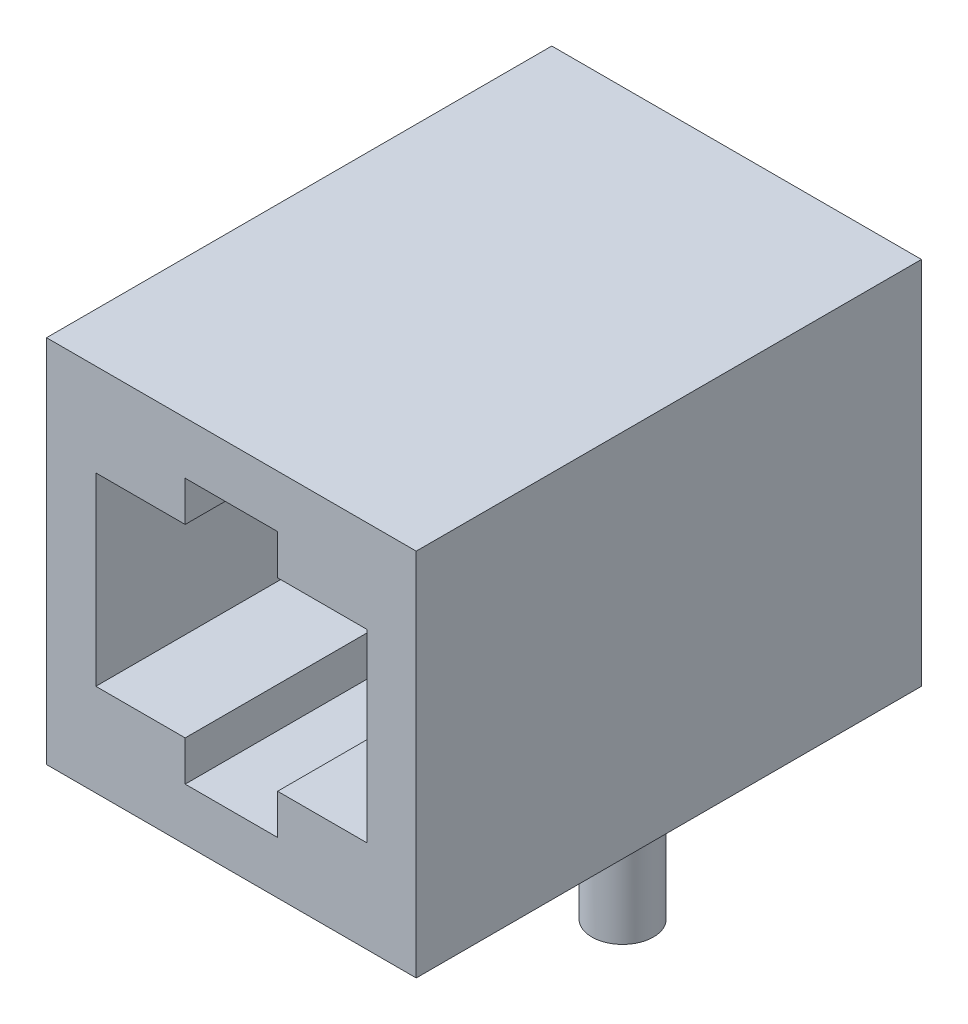
SolidWorks part; units mm, degrees
ref_plane "Front Plane" through (0, 0, 0) normal (0, 0, 1) x (1, 0, 0)
ref_plane "Top Plane" through (0, 0, 0) normal (0, 1, 0) x (1, 0, 0)
ref_plane "Right Plane" through (0, 0, 0) normal (1, 0, 0) x (0, 0, -1)
sketch "Sketch1" plane through (0, 0, 0) normal (0, 0, 1) x (1, 0, 0)
  line L1 (7.62, -7.62) -> (-7.62, -7.62)
  line L2 (7.62, -7.62) -> (7.62, 7.62)
  line L3 (7.62, 7.62) -> (-7.62, 7.62)
  line L4 (-7.62, -7.62) -> (-7.62, 7.62)
  line L5 (7.62, -7.62) -> (-7.62, 7.62) construction
  line L6 (7.62, 7.62) -> (-7.62, -7.62) construction
  point P0 (0, 0)
  dimension "D1" = 15.24
  dimension "D2" = 15.24
extrude "Boss-Extrude1" add sketch "Sketch1" along normal blind 20.828
sketch "Sketch2" plane through (0, 0, 20.828) normal (0, 0, 1) x (1, 0, 0)
  line L0 (-7.62, 7.62) -> (-7.62, -7.62) construction
  line L1 (5.588, -3.81) -> (1.905, -3.81)
  line L2 (5.588, -3.81) -> (5.588, 3.81)
  line L3 (5.588, 3.81) -> (1.905, 3.81)
  line L4 (-5.588, -3.81) -> (-5.588, 3.81)
  line L5 (5.588, -3.81) -> (-5.588, 3.81) construction
  line L6 (5.588, 3.81) -> (-5.588, -3.81) construction
  line L9 (-1.905, 3.81) -> (-1.905, 5.461)
  line L10 (-1.905, 5.461) -> (1.905, 5.461)
  line L11 (1.905, 3.81) -> (1.905, 5.461)
  line L13 (-1.905, -3.81) -> (-1.905, -5.461)
  line L14 (-1.905, -5.461) -> (1.905, -5.461)
  line L15 (1.905, -3.81) -> (1.905, -5.461)
  line L16 (-1.905, 3.81) -> (-5.588, 3.81)
  line L17 (-1.905, -3.81) -> (-5.588, -3.81)
  point P0 (0, 0)
  point P16 (0, 5.461)
  dimension "D1" = 2.032
  dimension "D2" = 7.62
  dimension "D3" = 3.81
  dimension "D4" = 1.651
extrude "Cut-Extrude1" cut sketch "Sketch2" against normal blind 18.288
sketch "Sketch3" plane through (0, -7.62, 0) normal (0, -1, 0) x (1, 0, 0)
  line L0 (-5.715, 10.414) -> (5.715, 10.414) construction
  line L3 (-7.62, 20.828) -> (-7.62, 0) construction
  circle A0 centre (-5.715, 10.414) radius 1.27
  circle A1 centre (5.715, 10.414) radius 1.27
  point P6 (-7.62, 10.414)
  point P7 (0, 10.414)
  dimension "D2" = 2.54
  dimension "D1" = 11.43
extrude "Boss-Extrude2" add sketch "Sketch3" along normal blind 4.064
